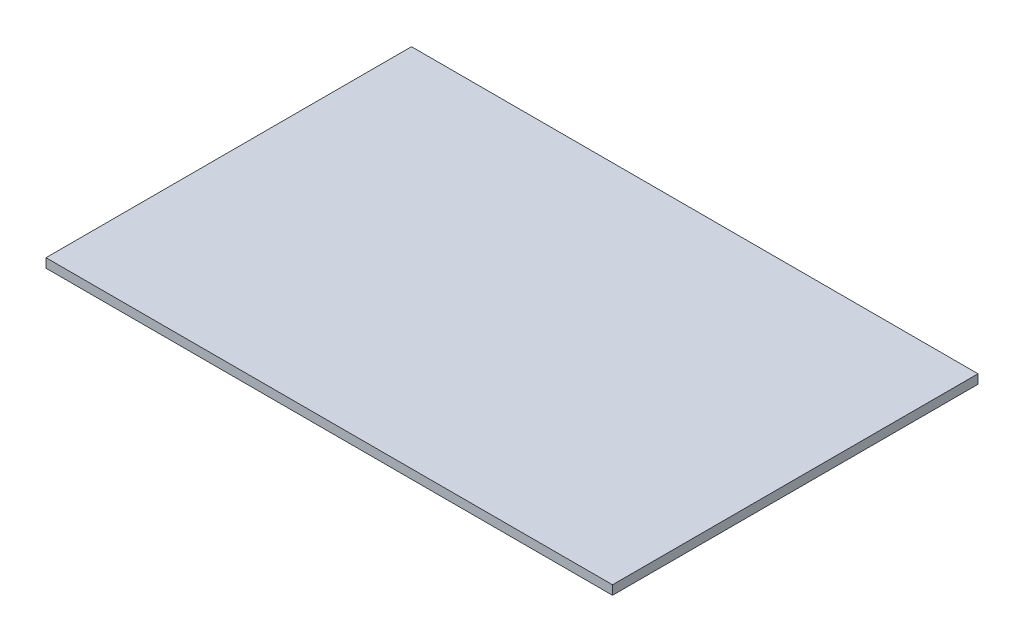
SolidWorks part; units mm, degrees
material "Oak"
ref_plane "Front" through (0, 0, 0) normal (0, 0, 1) x (1, 0, 0)
ref_plane "Top" through (0, 0, 0) normal (0, 1, 0) x (1, 0, 0)
ref_plane "Right" through (0, 0, 0) normal (1, 0, 0) x (0, 0, -1)
sketch "Sketch1" plane through (0, 0, 0) normal (0, 1, 0) x (1, 0, 0)
  line L1 (-196.85, 254) -> (196.85, 254)
  line L2 (-196.85, 254) -> (-196.85, 0)
  line L3 (-196.85, 0) -> (196.85, 0)
  line L4 (196.85, 254) -> (196.85, 0)
  point P4 (0, 0)
  dimension "D1" = 393.7
  dimension "D2" = 254
extrude "Boss-Extrude1" add sketch "Sketch1" along normal blind 6.35
